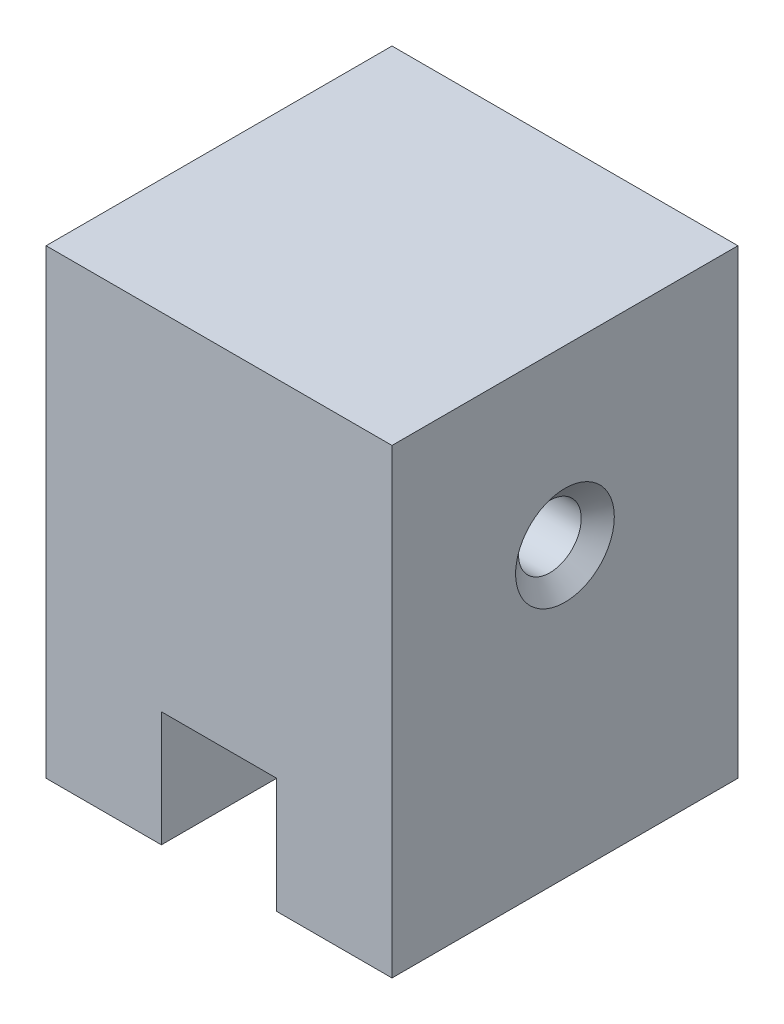
SolidWorks part; units mm, degrees
material "AISI 304"
ref_plane "Front Plane" through (0, 0, 0) normal (0, 0, 1) x (1, 0, 0)
ref_plane "Top Plane" through (0, 0, 0) normal (0, 1, 0) x (1, 0, 0)
ref_plane "Right Plane" through (0, 0, 0) normal (1, 0, 0) x (0, 0, -1)
sketch "Sketch1" plane through (0, 0, 0) normal (0, 1, 0) x (1, 0, 0)
  line L1 (-9.525, -9.525) -> (9.525, -9.525)
  line L2 (-9.525, -9.525) -> (-9.525, 9.525)
  line L3 (-9.525, 9.525) -> (9.525, 9.525)
  line L4 (9.525, -9.525) -> (9.525, 9.525)
  line L5 (-9.525, -9.525) -> (9.525, 9.525) construction
  line L6 (-9.525, 9.525) -> (9.525, -9.525) construction
  point P0 (0, 0)
  dimension "D1" = 19.05
extrude "Boss-Extrude1" add sketch "Sketch1" along normal blind 25.4
sketch "Sketch2" plane through (0, 0, 9.525) normal (0, 0, 1) x (1, 0, 0)
  line L0 (-9.525, 0) -> (9.525, 0) construction
  line L1 (-3.175, 0) -> (3.175, 0)
  line L2 (-3.175, 0) -> (-3.175, 6.35)
  line L3 (-3.175, 6.35) -> (3.175, 6.35)
  line L4 (3.175, 0) -> (3.175, 6.35)
  point P6 (0, 6.35)
  point P7 (0, 0)
  dimension "D1" = 6.35
  dimension "D2" = 6.35
extrude "Cut-Extrude1" cut sketch "Sketch2" against normal through all
hole_wizard "#8-32 Tapped Hole1" positions "Sketch3" profile "Sketch4" tap size "#8-32" standard "ANSI Inch" end condition through all
sketch "Sketch3" plane through (9.525, 0, 0) normal (-1, 0, 0) x (0, 0, 1)
  line L1 (9.525, 25.4) -> (-9.525, 25.4) construction
  point P0 (0, 15.875)
  point P5 (0, 0)
  point P11 (4.5987, 25.4)
  dimension "D1" = 9.525
sketch "Sketch4" plane through (9.525, 15.875, 0) normal (0, 1, 0) x (0, 0, -1)
  line L0 (0, 0) -> (0, 19.05)
  line L1 (0, 19.05) -> (1.7272, 19.05)
  line L2 (1.7272, 19.05) -> (1.7272, 0.8312)
  line L3 (1.7272, 0.8312) -> (2.7178, 0)
  line L5 (2.7178, 0) -> (0, 0)
  line L6 (-1.7272, 0.8312) -> (-2.7178, 0) construction
  line L11 (0, -6.35) -> (0, 107.95) construction
  dimension "Thru Tap Drill Dia." = 3.4544
  dimension "Thru Tap Drill Depth" = 19.05
  dimension "Near C'Sink Dia." = 5.4356
  dimension "Near C'Sink Angle" = 100
cosmetic thread "Hole Thread1" parameters "D2"=4.1656
